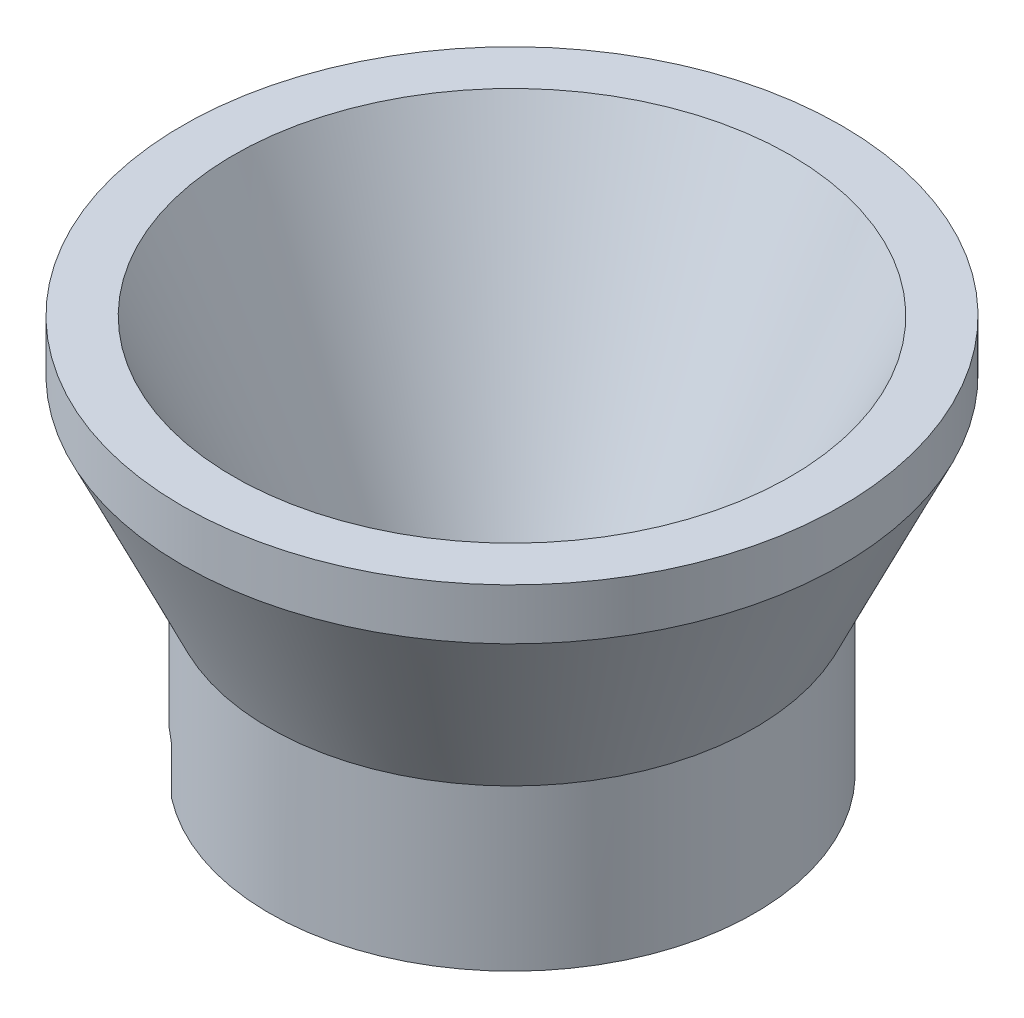
SolidWorks part; units mm, degrees
ref_plane "Front Plane" through (0, 0, 0) normal (0, 0, 1) x (1, 0, 0)
ref_plane "Top Plane" through (0, 0, 0) normal (0, 1, 0) x (1, 0, 0)
ref_plane "Right Plane" through (0, 0, 0) normal (1, 0, 0) x (0, 0, -1)
sketch "Sketch1" plane through (0, 0, 0) normal (1, 0, 0) x (0, 0, -1)
  line L0 (0, 0) -> (0, 8.75) construction
  line L1 (-7.5, 0) -> (-7.5, 1.85)
  line L2 (-7.5, 1.85) -> (-5.85, 3.5)
  line L3 (-5.85, 3.5) -> (-5.25, 3.5)
  line L4 (-7.5, 0) -> (-9.5, 0)
  line L5 (-12.9, 13.5) -> (-12.9, 15.5)
  line L6 (-12.9, 15.5) -> (-10.9, 15.5)
  line L7 (-10.9, 15.5) -> (-5.25, 3.5)
  line L8 (-12.9, 13.5) -> (-9.5, 6.2788)
  line L9 (-9.5, 6.2788) -> (-9.5, 0)
  point P4 (-5.55, 3.5)
  dimension "D1" = 135
  dimension "D2" = 11.7
  dimension "D3" = 10.5
  dimension "D4" = 12
  dimension "D5" = 7.5
  dimension "D6" = 2
  dimension "D7" = 2
  dimension "D8" = 2
  dimension "D9" = 12.9
  dimension "D10" = 15.5
revolve "Revolve1" add sketch "Sketch1" angle 360 about L0
sketch "Sketch2" plane through (0, 0, 0) normal (1, 0, 0) x (0, 0, -1)
  line L0 (-9.5, 0) -> (9.5, 0) construction
  line L1 (-7.5, 0) -> (7.5, 0)
  line L2 (-7.5, 0) -> (-7.5, 1.85)
  line L3 (-7.5, 1.85) -> (7.5, 1.85)
  line L4 (7.5, 0) -> (7.5, 1.85)
  line L8 (7.5, 1.85) -> (-7.5, 1.85) construction
  dimension "D1" = 15
extrude "Cut-Extrude1" cut sketch "Sketch2" against normal up to surface (5.831 mm away)
